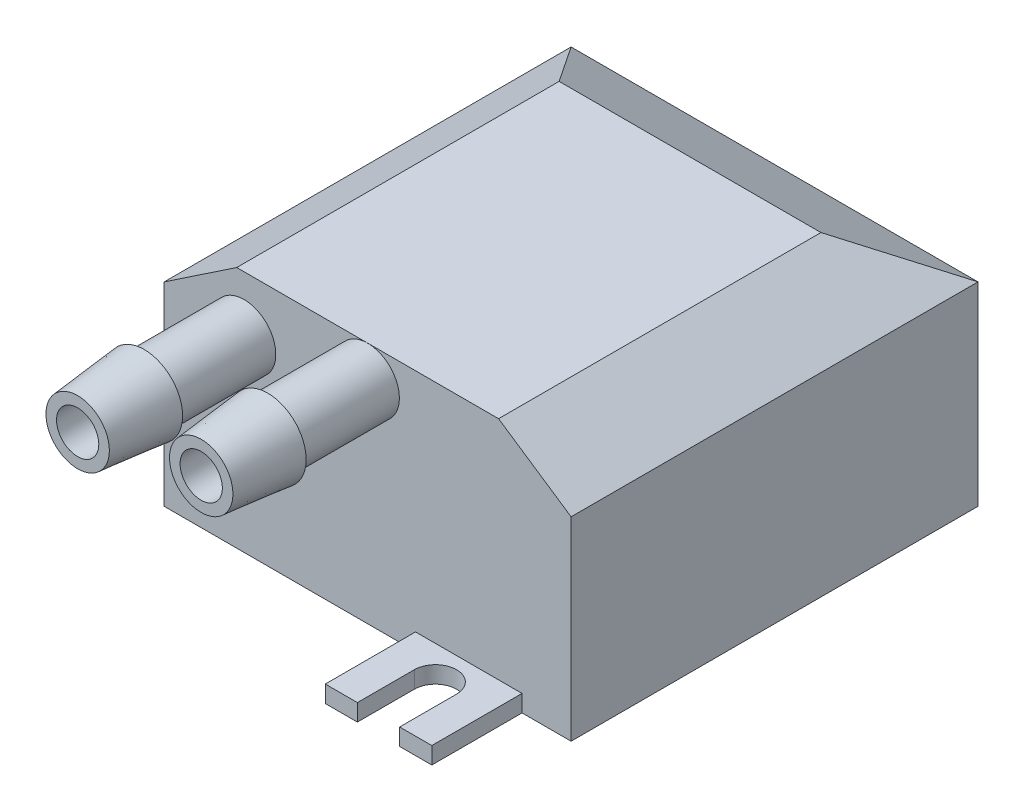
SolidWorks part; units mm, degrees
ref_plane "Front Plane" through (0, 0, 0) normal (0, 0, 1) x (1, 0, 0)
ref_plane "Top Plane" through (0, 0, 0) normal (0, 1, 0) x (1, 0, 0)
ref_plane "Right Plane" through (0, 0, 0) normal (1, 0, 0) x (0, 0, -1)
sketch "Sketch1" plane through (0, 0, 0) normal (0, 1, 0) x (1, 0, 0)
  line L1 (-30.5594, 30.5594) -> (30.5594, 30.5594)
  line L2 (-30.5594, 30.5594) -> (-30.5594, -30.5594)
  line L3 (-30.5594, -30.5594) -> (30.5594, -30.5594)
  line L4 (30.5594, 30.5594) -> (30.5594, -30.5594)
  dimension "D1" = 61.1187
  dimension "D2" = 30.5594
  dimension "D3" = 61.1187
  dimension "D4" = 30.5594
extrude "Extrude1" add sketch "Sketch1" along normal blind 36.5125
sketch "Sketch3" plane through (0, 0, 30.5594) normal (0, 0, 1) x (1, 0, 0)
  line L0 (19.6648, 36.5125) -> (30.5594, 29.1971)
  line L2 (0, 0) -> (0, 39) construction
  line L3 (-30.5594, 29.1971) -> (-30.5594, 0)
  line L4 (-30.5594, 36.5125) -> (30.5594, 36.5125) construction
  line L5 (30.5594, 29.1971) -> (30.5594, 0)
  line L6 (30.5594, 0) -> (-30.5594, 0)
  line L7 (-19.6648, 36.5125) -> (-30.5594, 29.1971)
  line L8 (-19.6648, 36.5125) -> (19.6648, 36.5125)
extrude "Cut-Extrude7" cut sketch "Sketch3" against normal blind 62 flip side to cut
sketch "Sketch4" plane through (30.5594, 0, 0) normal (1, 0, 0) x (0, 0, -1)
  line L1 (-30.5594, 36.5125) -> (17.8672, 36.5125)
  line L2 (30.5594, 36.5125) -> (-30.5594, 36.5125) construction
  line L3 (17.8672, 36.5125) -> (30.5594, 29.1971)
  line L4 (30.5594, 29.1971) -> (30.5594, 0)
  line L5 (30.5594, 0) -> (-30.5594, 0)
  line L10 (-30.5594, 36.5125) -> (-30.5594, 0)
extrude "Cut-Extrude8" cut sketch "Sketch4" against normal blind 250 flip side to cut
sketch "Sketch2" plane through (0, 0, 30.5594) normal (0, 0, 1) x (1, 0, 0)
  line L0 (0, 36.5125) -> (0, 0) construction
  circle A0 centre (0, 31.7413) radius 3.175
  circle A1 centre (0, 31.7413) radius 4.7625
extrude "Extrude2" add sketch "Sketch2" along normal blind 25
sketch "Sketch5" plane through (0, 0, 30.5594) normal (0, 0, 1) x (1, 0, 0)
  line L0 (-30.5594, 29.1971) -> (-30.5594, 0) construction
  circle A0 centre (-18.5594, 28.143) radius 4.7625
  circle A1 centre (-18.5594, 28.143) radius 3.175
  dimension "D1" = 12
extrude "Extrude3" add sketch "Sketch5" along normal blind 25
sketch "Sketch6" plane through (0, 0, 0) normal (0, -1, 0) x (1, 0, 0)
  line L0 (-30.5594, 30.5594) -> (30.5594, 30.5594) construction
  line L1 (7.1914, 30.5594) -> (23.1934, 30.5594)
  line L2 (7.1914, 30.5594) -> (7.1914, 44.1166)
  line L4 (23.1934, 30.5594) -> (23.1934, 44.1166)
  line L10 (30.5594, 30.5594) -> (30.5594, -30.5594) construction
  line L14 (7.1914, 44.1166) -> (12.0174, 44.1166)
  line L15 (12.0174, 44.1166) -> (12.0174, 35.5645)
  line L16 (23.1934, 44.1166) -> (18.3674, 44.1166)
  line L17 (18.3674, 44.1166) -> (18.3674, 35.5645)
  arc A0 (12.0174, 35.5645) -> (18.3674, 35.5645) centre (15.1924, 35.5645) ccw
  dimension "D1" = 6.35
  dimension "D3" = 16.002
  dimension "D5" = 23.368
  dimension "D8" = 4.826
extrude "Extrude4" add sketch "Sketch6" against normal blind 2.54
sketch "Sketch7" plane through (0, 0, 55.5594) normal (0, 0, 1) x (1, 0, 0)
  circle A0 centre (0, 31.7413) radius 4.7625
  circle A1 centre (0, 31.7413) radius 5.76
extrude "Extrude5" add sketch "Sketch7" against normal blind 10
sketch "Sketch8" plane through (0, 0, 0) normal (1, 0, 0) x (0, 0, -1)
  line L0 (-55.5594, 36.5038) -> (-55.5594, 37.5013)
  line L2 (-55.5594, 37.5013) -> (-45.5594, 37.5013)
  line L4 (-55.5594, 37.5013) -> (-55.5594, 25.9813) construction
  line L5 (-55.5594, 36.5038) -> (-45.5594, 37.5013)
  line L6 (-55.5594, 31.7413) -> (-45.5594, 31.7413) construction
  line L7 (-45.5594, 26.9788) -> (-45.5594, 36.5038) construction
revolve "Cut-Revolve2" cut sketch "Sketch8" angle 360 about L6
sketch3d "3DSketch1" plane through (0, 0, 0) normal (0, 0, 1) x (1, 0, 0)
  dimension "D1" = 12
sketch "Sketch10" plane through (-18.5594, 0, 0) normal (1, 0, 0) x (0, 0, -1)
  line L0 (-55.5594, 28.143) -> (-45.5594, 28.143) construction
  line L2 (-55.5594, 32.9055) -> (-55.5594, 23.3805) construction
  line L4 (-55.5594, 32.9055) -> (-45.5594, 32.9055)
  line L6 (-30.5594, 32.9055) -> (-55.5594, 32.9055) construction
  line L7 (-45.5594, 32.9055) -> (-45.5594, 33.9055)
  line L8 (-45.5594, 25.9813) -> (-45.5594, 37.5013) construction
  line L9 (-45.5594, 33.9055) -> (-55.5594, 32.9055)
revolve "Revolve1" add sketch "Sketch10" angle 360 about L0
